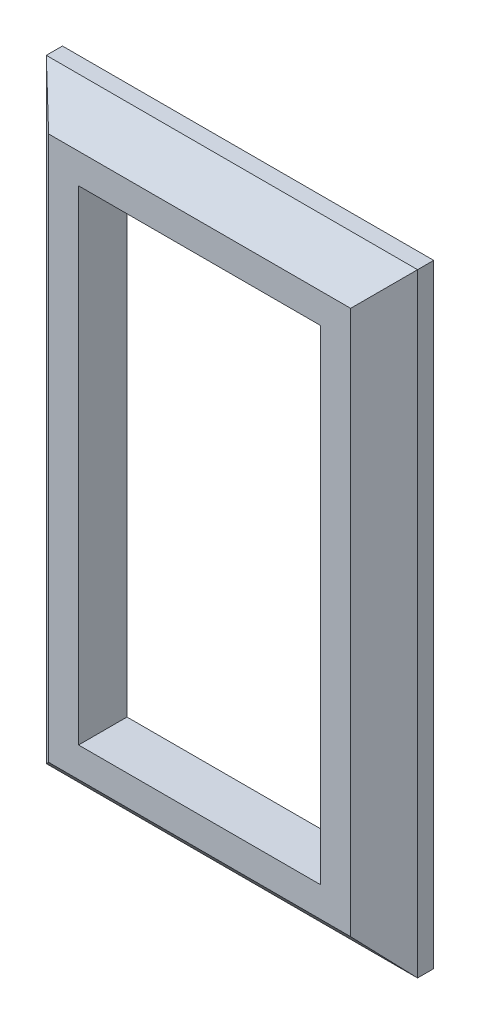
SolidWorks part; units mm, degrees
ref_plane "Plano frontal" through (0, 0, 0) normal (0, 0, 1) x (1, 0, 0)
ref_plane "Plano superior" through (0, 0, 0) normal (0, 1, 0) x (1, 0, 0)
ref_plane "Plano direito" through (0, 0, 0) normal (1, 0, 0) x (0, 0, -1)
sketch "Esboço1" plane through (0, 0, 0) normal (0, 0, 1) x (1, 0, 0)
  line L1 (7.5, -15) -> (-7.5, -15)
  line L2 (7.5, -15) -> (7.5, 15)
  line L3 (7.5, 15) -> (-7.5, 15)
  line L4 (-7.5, -15) -> (-7.5, 15)
  line L5 (7.5, -15) -> (-7.5, 15) construction
  line L6 (7.5, 15) -> (-7.5, -15) construction
  line L7 (11.5, -19) -> (-11.5, -19)
  line L8 (11.5, -19) -> (11.5, 19)
  line L9 (11.5, 19) -> (-11.5, 19)
  line L10 (-11.5, -19) -> (-11.5, 19)
  line L11 (11.5, -19) -> (-11.5, 19) construction
  line L12 (11.5, 19) -> (-11.5, -19) construction
  point P0 (0, 0)
  point P6 (0, 0)
extrude "Ressalto-extrusão1" add sketch "Esboço1" along normal blind 3
chamfer "Chanfro1" distance 2 angle 47 4 edges at (0, 19, 3) (11.5, 0, 3) (0, -19, 3) (-11.5, 0, 3)
